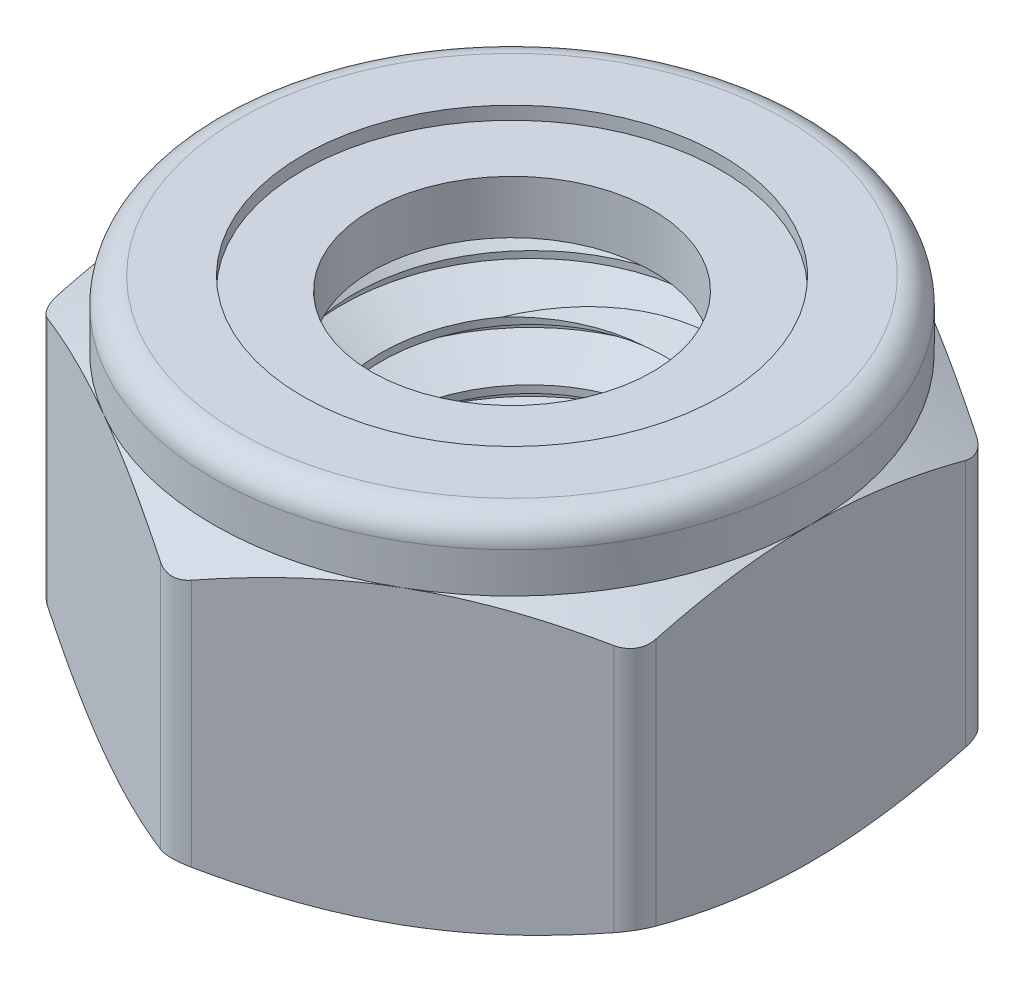
SolidWorks part; units mm, degrees
ref_plane "Front Plane" through (0, 0, 0) normal (0, 0, 1) x (1, 0, 0)
ref_plane "Top Plane" through (0, 0, 0) normal (0, 1, 0) x (1, 0, 0)
ref_plane "Right Plane" through (0, 0, 0) normal (1, 0, 0) x (0, 0, -1)
sketch "Sketch1" plane through (0, 0, 0) normal (0, 0, 1) x (1, 0, 0)
  line L0 (-5, -3) -> (5, -3) construction
  line L1 (-5, -3) -> (-5, 1.8917) construction
  line L2 (-5, 1.8917) -> (5, 1.8917) construction
  line L7 (5, 1.8917) -> (5, -3) construction
  line L8 (0, 3) -> (0, -3) construction
  line L9 (-3, 3) -> (-3, -3) construction
  line L10 (3, 3) -> (3, -3) construction
  line L11 (-3, 3) -> (3, 3) construction
  line L14 (5, -3) -> (5.7722, -2.5542) construction
  line L15 (5, 1.8917) -> (5, 3) construction
  line L16 (5, 3) -> (3, 3) construction
  line L17 (5.7722, -2.5542) -> (5.7722, 1.4458) construction
  line L18 (-5, 1.8917) -> (-5, 3) construction
  line L19 (-5, 3) -> (-3, 3) construction
  line L20 (5.7722, 1.4458) -> (5, 1.8917) construction
  line L21 (-3, -3) -> (-3, -3.875) construction
  line L22 (-3, -3.875) -> (-2.2422, -3.4375) construction
  line L23 (-2.2422, -3.4375) -> (-3, -3) construction
  line L24 (-3.1083, -2.9375) -> (-3.1083, -3.9375) construction
  line L25 (-3.1083, -2.9375) -> (-3, -3) construction
  line L26 (-3, -3.875) -> (-3.1083, -3.9375) construction
  line L27 (-2.3505, -3.375) -> (-2.3505, -3.5) construction
  line L28 (-3, -3.4375) -> (-3.1083, -3.4375) construction
  line L29 (-2.3505, -3.4375) -> (-2.2422, -3.4375) construction
  dimension "Width | s" = 10
  dimension "Thread Diameter" = 6
  dimension "Height | h" = 6
  dimension "D1" = 11.5444
  dimension "D2" = 30
  dimension "Flats Height" = 4
  dimension "Thread Pitch" = 1
  dimension "D4" = 0.125
sketch "Sketch2" plane through (0, 0, 0) normal (0, 1, 0) x (1, 0, 0)
  line L0 (0, 0) -> (2.5, 4.3301) construction
  line L1 (5, 2.8868) -> (0, 5.7735)
  line L2 (0, 5.7735) -> (-5, 2.8868)
  line L3 (-5, 2.8868) -> (-5, -2.8868)
  line L4 (-5, -2.8868) -> (0, -5.7735)
  line L5 (0, -5.7735) -> (5, -2.8868)
  line L6 (5, -2.8868) -> (5, 2.8868)
  line L7 (0, 0) -> (5, 2.8868) construction
  circle A0 centre (0, 0) radius 5 construction
  circle A1 centre (0, 0) radius 5.7735 construction
extrude "Boss-Extrude1" add sketch "Sketch2" against normal up to vertex (3 mm away) from vertex at 1.8917 starting at point (5, 1.8917, 0)
sketch "Sketch3" plane through (0, 0, 0) normal (0, 0, 1) x (1, 0, 0)
  line L3 (3, 3.0464) -> (5.7822, 1.4401)
  line L4 (3, 3) -> (3, -3) construction
  line L5 (3, -4.1547) -> (5.7822, -2.5484)
  line L6 (5.7822, -2.5484) -> (5.7822, -4.1547)
  line L7 (5.7822, -4.1547) -> (3, -4.1547)
  line L8 (3, 3.0464) -> (5.7822, 3.0464)
  line L10 (5.7822, 1.4401) -> (5.7822, 3.0464)
  dimension "D1" = 0.01
revolve "Cut-Revolve1" cut sketch "Sketch3" angle 360 about L8
fillet "Fillet1" radius 0.5148 6 edges at (-5, -0.5542, -2.8868) (-5, -0.5542, 2.8868) (0, -0.5542, 5.7735) (0, -0.5542, -5.7735) (5, -0.5542, -2.8868) (5, -0.5542, 2.8868)
sketch "Sketch5" plane through (0, 0, 0) normal (0, 0, 1) x (1, 0, 0)
  line L0 (-3.5, -3) -> (-3, -2.5)
  line L1 (-5, -3) -> (5, -3) construction
  line L2 (-3, 3) -> (-3, -3) construction
  line L3 (-3, -2.5) -> (-3, 1.3917)
  line L4 (-3, 1.3917) -> (-3.5, 1.8917)
  line L5 (-5, 1.8917) -> (5, 1.8917) construction
  line L6 (-3.5, 1.8917) -> (0, 1.8917)
  line L7 (0, 1.8917) -> (0, -3)
  line L8 (0, -3) -> (-3.5, -3)
  line L9 (0, 3) -> (0, -3) construction
  dimension "D1" = 45
  dimension "D2" = 0.5
revolve "Cut-Revolve2" cut sketch "Sketch5" angle 360 about L8
sketch "Sketch4" plane through (0, 0, 0) normal (0, 0, 1) x (1, 0, 0)
  line L0 (-3.5, 3) -> (-4.5625, 3)
  line L1 (-5, 3) -> (-3, 3) construction
  line L2 (-5, 2.5625) -> (-5, 1.8917)
  line L4 (-4.5625, 3) -> (-4.5625, 2.5625) construction
  line L5 (-2.6211, -3.2188) -> (-2.6211, -3.6563) construction
  line L6 (-2.2422, -3.4375) -> (-3, -3) construction
  line L7 (-3, -3.875) -> (-2.2422, -3.4375) construction
  line L8 (-5, 1.8917) -> (-4.7812, 1.8917)
  line L10 (-3.5, 2.7812) -> (-3.5, 3)
  line L11 (-3.5, 2.7812) -> (-4.5625, 2.7812)
  line L12 (-4.7812, 2.5625) -> (-4.7812, 1.8917)
  arc A0 (-5, 2.5625) -> (-4.5625, 3) centre (-4.5625, 2.5625) cw
  arc A1 (-4.5625, 2.7812) -> (-4.7812, 2.5625) centre (-4.5625, 2.5625) ccw
revolve "Revolve1" add sketch "Sketch4" angle 360 about L8
sketch "Sketch6" plane through (0, 0, 0) normal (0, 0, 1) x (1, 0, 0)
  line L0 (-5, 1.8917) -> (5, 1.8917) construction
  line L1 (-4.5625, 2.7812) -> (-2.3505, 2.7812)
  line L2 (-4.7812, 2.5625) -> (-4.7812, 1.8917)
  line L3 (-4.7812, 1.8917) -> (-2.3505, 1.8917)
  line L4 (-2.3505, 2.7812) -> (-2.3505, 1.8917)
  arc A0 (-4.5625, 2.7812) -> (-4.7812, 2.5625) centre (-4.5625, 2.5625) ccw
revolve "Revolve2" add sketch "Sketch6" angle 360 about L8
sketch "Sketch7" plane through (0, -3, 0) normal (0, 1, 0) x (-1, 0, 0)
  line L0 (3, 0) -> (-3, 0) construction
  line L1 (0, 0) -> (-2.1213, -2.1213) construction
  circle A0 centre (0, 0) radius 3
  point P7 (-2.1213, -2.1213)
  dimension "D1" = 225
curve "Helix/Spiral1" pitch 1 height 6 turns 6
sketch "Sketch8" plane through (0, 0, 0) normal (0, 0, 1) x (1, 0, 0)
  line L0 (-3.0541, -2.9688) -> (-3.0541, -3.9062)
  line L1 (-3.1083, -2.9375) -> (-3, -3) construction
  line L2 (-3, -3.875) -> (-3.1083, -3.9375) construction
  line L3 (-3.0541, -3.9062) -> (-2.3505, -3.5)
  line L4 (-2.3505, -3.5) -> (-2.3505, -3.375)
  line L5 (-2.3505, -3.375) -> (-3.0541, -2.9688)
sweep "Sweep1" add profiles "Sketch8" path "Helix/Spiral1"
sketch "Sketch9" plane through (0, 0, 0) normal (0, 0, 1) x (1, 0, 0)
  line L0 (-3.5, 3.2188) -> (-3.5, 1.8917)
  line L1 (-3.5, 1.8917) -> (-2.2422, 0.6339)
  line L2 (-2.2422, 0.6339) -> (-2.2422, 3.2188)
  line L4 (-2.2422, 3.2188) -> (-3.5, 3.2188)
  line L5 (-2.2422, -1.7422) -> (-3.5, -3)
  line L6 (-3.5, -3) -> (-3.5, -3.9375)
  line L7 (-3.5, -3.9375) -> (-2.2422, -3.9375)
  line L8 (-2.2422, -3.9375) -> (-2.2422, -1.7422)
  line L9 (-2.8711, 3.2188) -> (-2.8711, 3) construction
  line L10 (-3, 3) -> (3, 3) construction
  line L12 (-3.5, 2.7812) -> (-3.5, 3) construction
revolve "Cut-Revolve3" cut sketch "Sketch9" angle 360 about L8
equation "\"D1@Sketch1\"=\"Width | s@Sketch1\"*(1.15+.04/9)"
equation "\"D1@Fillet1\"=(\"D1@Sketch1\"-\"Width | s@Sketch1\")/3"
equation "\"D4@Sketch1\" = \"Thread Pitch@Sketch1\" / 8"
equation "\"D2@Sketch5\"=\"Thread Pitch@Sketch1\"*.5"
equation "\"D3@Helix/Spiral1\"=\"Height | h@Sketch1\""
equation "\"D4@Helix/Spiral1\"=\"Thread Pitch@Sketch1\""
